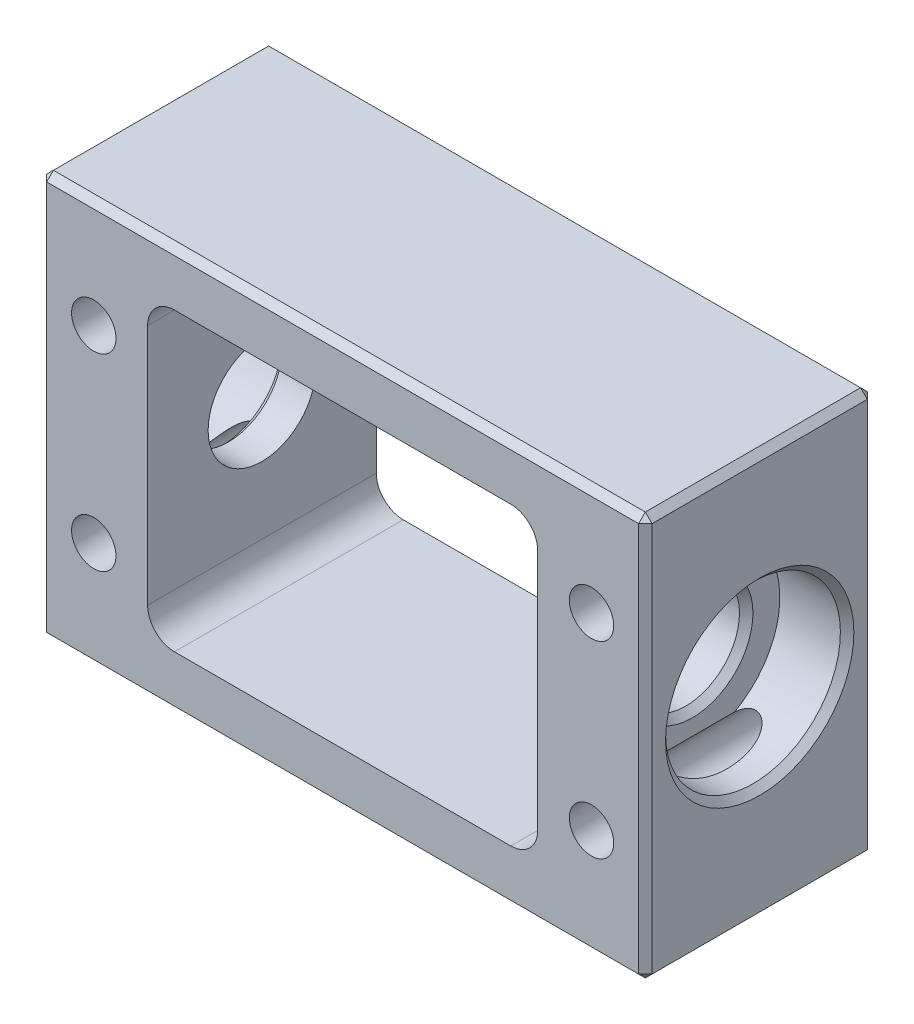
SolidWorks part; units mm, degrees
material "6061 合金"
ref_plane "前视基准面" through (0, 0, 0) normal (0, 0, 1) x (1, 0, 0)
ref_plane "上视基准面" through (0, 0, 0) normal (0, 1, 0) x (1, 0, 0)
ref_plane "右视基准面" through (0, 0, 0) normal (1, 0, 0) x (0, 0, -1)
sketch "草图1" plane through (0, 0, 0) normal (0, 0, 1) x (1, 0, 0)
  line L1 (-22.5, -15) -> (22.5, -15)
  line L2 (-22.5, -15) -> (-22.5, 15)
  line L3 (-22.5, 15) -> (22.5, 15)
  line L4 (22.5, -15) -> (22.5, 15)
  line L5 (0, 15) -> (0, -15) construction
  line L6 (-22.5, 0) -> (22.5, 0) construction
  point P0 (0, 0)
  dimension "D1" = 30
  dimension "D2" = 45
extrude "凸台-拉伸1" add sketch "草图1" along normal mid plane 17
sketch "草图2" plane through (22.5, 0, 0) normal (1, 0, 0) x (0, 0, -1)
  circle A0 centre (0, 0) radius 6.5
  dimension "D1" = 13
extrude "切除-拉伸1" cut sketch "草图2" against normal blind 5
mirror "镜向1" about plane through (0, 0, 0) normal (1, 0, 0) of "切除-拉伸1"
sketch "草图3" plane through (17.5, 0, 0) normal (1, 0, 0) x (0, 0, -1)
  circle A0 centre (0, 0) radius 4
  dimension "D1" = 8
extrude "切除-拉伸2" cut sketch "草图3" against normal blind 53
chamfer "倒角1" distance 0.5 angle 45 4 edges at (17.5, 0, -4) (22.5, 0, -6.5) (-22.5, 0, -6.5) (-17.5, 0, 4)
sketch "草图4" plane through (0, 0, -8.5) normal (0, 0, -1) x (-1, 0, 0)
  line L0 (-22.5, 15) -> (22.5, 15) construction
  line L1 (-18.5, -7) -> (18.5, -7)
  line L2 (-18.5, -7) -> (-18.5, 7)
  line L3 (-18.5, 7) -> (18.5, 7)
  line L4 (18.5, -7) -> (18.5, 7)
  line L5 (0, 7) -> (0, -7) construction
  line L6 (-18.5, 0) -> (18.5, 0) construction
  line L7 (22.5, 15) -> (22.5, -15) construction
  point P0 (0, 0)
  dimension "D1" = 8
  dimension "D2" = 4
hole_wizard "M4 螺纹孔1" positions "草图5" profile "草图6" tap size "M4" standard "GB" end condition through all
sketch "草图5" plane through (0, 0, -8.5) normal (0, 0, -1) x (-1, 0, 0)
  point P0 (-18.5, 7)
  point P3 (18.5, 7)
  point P6 (-18.5, -7)
  point P9 (18.5, -7)
sketch "草图6" plane through (18.5, 7, -8.5) normal (1, 0, 0) x (0, 1, 0)
  line L0 (0, 0) -> (0, 17)
  line L1 (0, 17) -> (1.65, 17)
  line L2 (1.65, 17) -> (1.65, 0)
  line L5 (1.65, 0) -> (0, 0)
  line L11 (0, -6.35) -> (0, 107.95) construction
  dimension "通孔螺纹孔钻头直径" = 3.3
  dimension "通孔螺纹孔钻头深度" = 17
cosmetic thread "孔螺蚊线1" parameters "D2"=4
cosmetic thread "孔螺蚊线2" parameters "D2"=4
cosmetic thread "孔螺蚊线3" parameters "D2"=4
cosmetic thread "孔螺蚊线4" parameters "D2"=4
sketch "草图7" plane through (0, 0, -8.5) normal (0, 0, -1) x (-1, 0, 0)
  line L0 (-22.5, 15) -> (22.5, 15) construction
  line L1 (-14.5, -11) -> (14.5, -11)
  line L2 (-14.5, -11) -> (-14.5, 11)
  line L3 (-14.5, 11) -> (14.5, 11)
  line L4 (14.5, -11) -> (14.5, 11)
  line L5 (0, 11) -> (0, -11) construction
  line L6 (-14.5, 0) -> (14.5, 0) construction
  circle A0 centre (18.5, 7) radius 1.65 construction
  point P0 (0, 0)
  dimension "D1" = 4
  dimension "D2" = 4
extrude "切除-拉伸3" cut sketch "草图7" against normal blind 53
fillet "圆角1" radius 2 4 edges at (-14.5, 11, 0) (-14.5, -11, 0) (14.5, -11, 0) (14.5, 11, 0)
chamfer "倒角2" distance 0.5 angle 45 12 edges at (-22.5, 15, 0) (-22.5, 0, 8.5) (-22.5, 0, -8.5) (-22.5, -15, 0) (0, -15, 8.5) (22.5, -15, 0) (0, -15, -8.5) (0, 15, 8.5) (22.5, 0, 8.5) (22.5, 0, -8.5) (0, 15, -8.5) (22.5, 15, 0)
